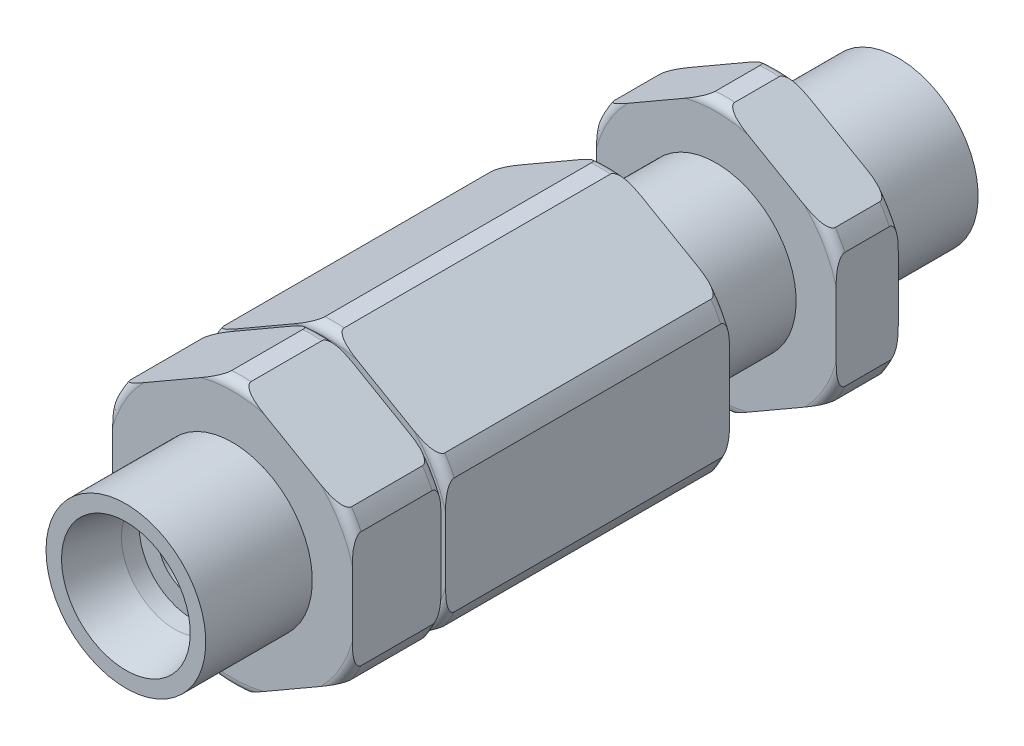
SolidWorks part; units mm, degrees
ref_plane "Plane1" through (0, 0, 0) normal (0, 0, 1) x (1, 0, 0)
ref_plane "Plane2" through (0, 0, 0) normal (0, 1, 0) x (1, 0, 0)
ref_plane "Plane3" through (0, 0, 0) normal (1, 0, 0) x (0, 0, -1)
sketch "Sketch1" plane through (0, 0, 0) normal (0, 0, 1) x (1, 0, 0)
  line L1 (13.5, -7.7942) -> (13.5, 7.7942)
  line L2 (13.5, 7.7942) -> (0, 15.5885)
  line L3 (0, 15.5885) -> (-13.5, 7.7942)
  line L4 (-13.5, 7.7942) -> (-13.5, -7.7942)
  line L5 (-13.5, -7.7942) -> (0, -15.5885)
  line L6 (0, -15.5885) -> (13.5, -7.7942)
  circle A0 centre (0, 0) radius 13.5 construction
  dimension "D1" = 27
extrude "Extrude1" add sketch "Sketch1" along normal blind 87
sketch "Sketch2" plane through (0, 0, 0) normal (1, 0, 0) x (0, 0, -1)
  line L0 (0, 0) -> (-87, 0) construction
  line L1 (-87, 7.7942) -> (-87, -7.7942) construction
  line L3 (-87, 15.5885) -> (0, 15.5885) construction
  line L4 (-87, 15.5885) -> (-87, 7.7942) construction
  line L5 (-87, 15.5885) -> (-87, 9)
  line L6 (-75, 14) -> (-75, 9)
  line L7 (-75, 9) -> (-87, 9)
  line L8 (-20.5, 14) -> (-20.5, 9)
  line L9 (-87, 15.5885) -> (0, 15.5885)
  line L10 (0, 15.5885) -> (0, 9)
  line L11 (0, 9) -> (-13.5, 9)
  line L12 (-32.5, 14) -> (-32.5, 9)
  line L13 (-13.5, 14) -> (-13.5, 9)
  line L14 (-20.5, 9) -> (-32.5, 9)
  line L15 (-74, 15) -> (-66, 15)
  line L16 (-19.5, 15) -> (-14.5, 15)
  line L17 (-65, 14) -> (-65, 9)
  line L18 (-65, 9) -> (-64.5, 9)
  line L19 (-64.5, 9) -> (-64.5, 14)
  line L20 (-63.5, 15) -> (-33.5, 15)
  arc A0 (-64.5, 14) -> (-63.5, 15) centre (-63.5, 14) cw
  arc A1 (-65, 14) -> (-66, 15) centre (-66, 14) ccw
  arc A2 (-74, 15) -> (-75, 14) centre (-74, 14) ccw
  arc A3 (-33.5, 15) -> (-32.5, 14) centre (-33.5, 14) cw
  arc A4 (-19.5, 15) -> (-20.5, 14) centre (-19.5, 14) ccw
  arc A5 (-14.5, 15) -> (-13.5, 14) centre (-14.5, 14) cw
  point P25 (-64.5, 15)
  point P32 (-32.5, 15)
  dimension "D9" = 1
  dimension "D1" = 12
  dimension "D2" = 18
  dimension "D3" = 42.5
  dimension "D4" = 7
  dimension "D5" = 12
  dimension "D6" = 30
  dimension "D7" = 0.5
  dimension "D8" = 10
revolve "Cut-Revolve1" cut sketch "Sketch2" angle 360 about L0
sketch "Sketch3" plane through (0, 0, 0) normal (1, 0, 0) x (0, 0, -1)
  line L0 (0, 0) -> (-88.1446, 0) construction
  line L1 (-87, 9) -> (-87, -9) construction
  line L2 (0, 7.25) -> (-5.5, 6)
  line L3 (0, -9) -> (0, 9) construction
  line L4 (-5.5, 6) -> (-7.5, 6)
  line L5 (-7.5, 6) -> (-7.5, 3.9)
  line L6 (-7.5, 3.9) -> (-79.5, 3.9)
  line L7 (-79.5, 3.9) -> (-79.5, 6)
  line L8 (-79.5, 6) -> (-81.5, 6)
  line L9 (-81.5, 6) -> (-87, 7.25)
  line L10 (-87, 7.25) -> (-87, 0)
  line L11 (0, 0) -> (0, 7.25)
  line L12 (0, 0) -> (-87, 0)
  dimension "D1" = 12
  dimension "D2" = 14.5
  dimension "D3" = 7.5
  dimension "D4" = 2
  dimension "D5" = 7.8
  dimension "D6" = 7.5
  dimension "D7" = 2
revolve "Cut-Revolve2" cut sketch "Sketch3" angle 360 about L0
